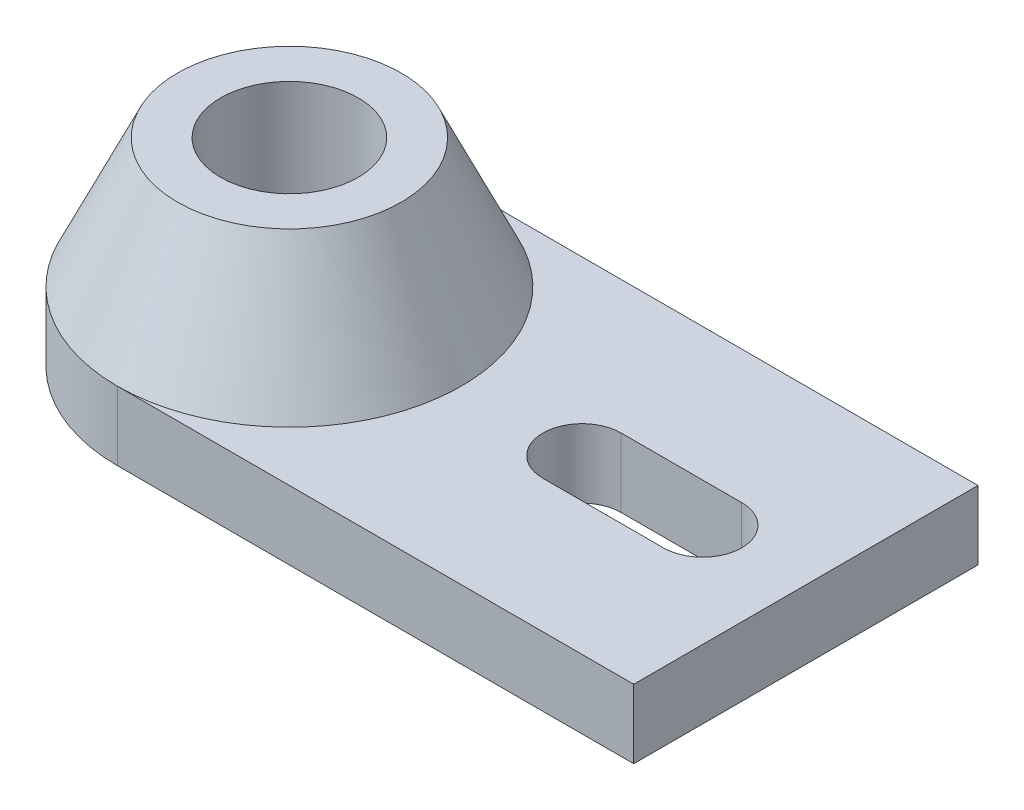
SolidWorks part; units mm, degrees
material "1060 Alloy"
ref_plane "Front Plane" through (0, 0, 0) normal (0, 0, 1) x (1, 0, 0)
ref_plane "Top Plane" through (0, 0, 0) normal (0, 1, 0) x (1, 0, 0)
ref_plane "Right Plane" through (0, 0, 0) normal (1, 0, 0) x (0, 0, -1)
sketch "Sketch1" plane through (0, 0, 0) normal (0, 1, 0) x (1, 0, 0)
  circle A0 centre (0, 0) radius 20
  dimension "D1" = 20
ref_plane "Plane1" through (0, 15, 0) normal (0, 1, 0) x (1, 0, 0)
sketch "Sketch2" plane through (0, 15, 0) normal (0, 1, 0) x (1, 0, 0)
  circle A0 centre (0, 0) radius 13
  dimension "D1" = 26
loft "Loft1" add profiles "Sketch2", "Sketch1"
sketch "Sketch5" plane through (0, 0, 0) normal (0, 1, 0) x (1, 0, 0)
  line L0 (0, 20) -> (60, 20)
  line L1 (60, 20) -> (60, -20)
  line L2 (60, -20) -> (0, -20)
  circle A0 centre (0, 0) radius 20 construction
  arc A2 (0, 20) -> (0, -20) centre (0, 0) ccw
  dimension "D1" = 60
extrude "Boss-Extrude1" add sketch "Sketch5" against normal blind 8 separate body
sketch "Sketch6" plane through (0, 0, 0) normal (0, 1, 0) x (1, 0, 0)
  line L0 (34, 0) -> (48, 0) construction
  line L1 (34, 4.551) -> (48, 4.551)
  line L2 (34, -4.551) -> (48, -4.551)
  line L3 (60, 20) -> (0, 20) construction
  line L4 (60, -20) -> (60, 20) construction
  arc A0 (34, 4.551) -> (34, -4.551) centre (34, 0) ccw
  arc A1 (48, -4.551) -> (48, 4.551) centre (48, 0) ccw
  point P2 (41, 0)
  dimension "D1" = 20
  dimension "D2" = 12
  dimension "D3" = 14
extrude "Cut-Extrude2" cut sketch "Sketch6" against normal up to next (8 mm away)
sketch "Sketch7" plane through (0, 15, 0) normal (0, 1, 0) x (1, 0, 0)
  circle A0 centre (0, 0) radius 8
  dimension "D1" = 16
extrude "Cut-Extrude3" cut sketch "Sketch7" against normal through all
